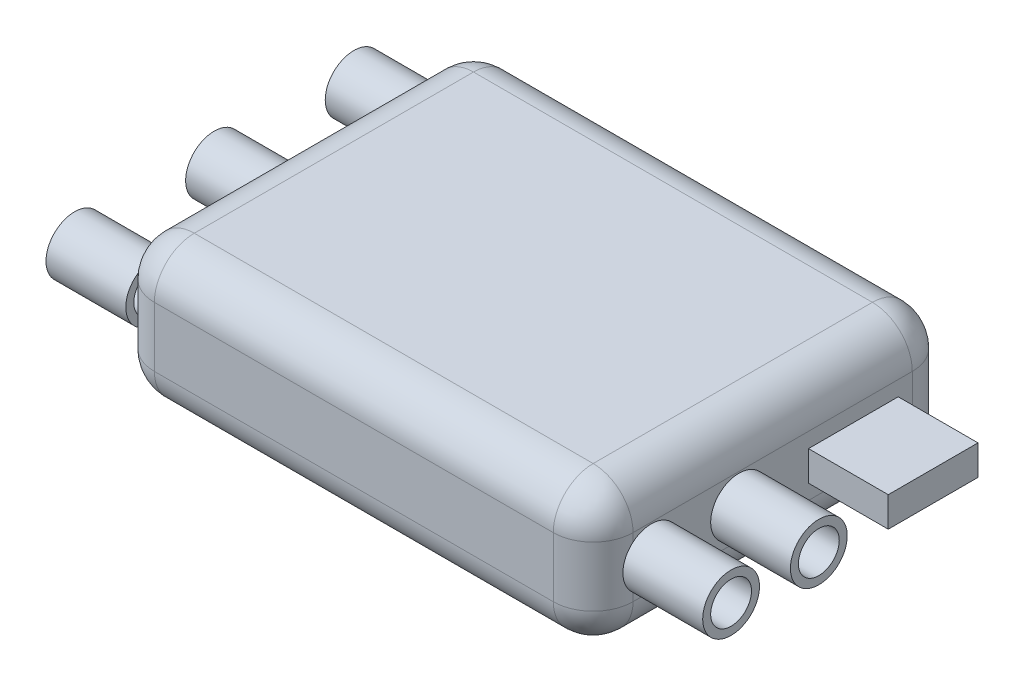
SolidWorks part; units mm, degrees
ref_plane "Front Plane" through (0, 0, 0) normal (0, 0, 1) x (1, 0, 0)
ref_plane "Top Plane" through (0, 0, 0) normal (0, 1, 0) x (1, 0, 0)
ref_plane "Right Plane" through (0, 0, 0) normal (1, 0, 0) x (0, 0, -1)
sketch "Sketch1" plane through (0, 0, 0) normal (0, 1, 0) x (1, 0, 0)
  line L1 (-10, 9) -> (10, 9)
  line L2 (-12, 7) -> (-12, -7)
  line L3 (-10, -9) -> (10, -9)
  line L4 (12, 7) -> (12, -7)
  line L5 (-12, 9) -> (12, -9) construction
  line L6 (-12, -9) -> (12, 9) construction
  arc A0 (10, -9) -> (12, -7) centre (10, -7) ccw
  arc A1 (-12, -7) -> (-10, -9) centre (-10, -7) ccw
  arc A2 (10, 9) -> (12, 7) centre (10, 7) cw
  arc A3 (-10, 9) -> (-12, 7) centre (-10, 7) ccw
  point P0 (0, 0)
  dimension "D3" = 2
  dimension "D1" = 24
  dimension "D2" = 18
extrude "Boss-Extrude1" add sketch "Sketch1" along normal blind 7
fillet "Fillet1" radius 2 16 edges at (12, 0, 0) (11.4142, 0, -8.4142) (0, 0, -9) (-11.4142, 0, -8.4142) (-12, 0, 0) (-11.4142, 0, 8.4142) (0, 0, 9) (11.4142, 0, 8.4142) (0, 7, 9) (-11.4142, 7, 8.4142) (-12, 7, 0) (-11.4142, 7, -8.4142) (0, 7, -9) (11.4142, 7, -8.4142) (12, 7, 0) (11.4142, 7, 8.4142)
sketch "Sketch2" plane through (-12, 0, 0) normal (-1, 0, 0) x (0, 0, 1)
  line L0 (-7, 3.5) -> (7, 3.5) construction
  line L1 (-7, 5) -> (-7, 2) construction
  line L2 (7, 5) -> (7, 2) construction
  circle A0 centre (-7, 3.5) radius 1.0342
  circle A1 centre (-7, 3.5) radius 1.4342
  circle A2 centre (0, 3.5) radius 1.0342
  circle A3 centre (0, 3.5) radius 1.4342
  circle A4 centre (7, 3.5) radius 1.0342
  circle A5 centre (7, 3.5) radius 1.4342
  dimension "D1" = 0.4
extrude "Boss-Extrude2" add sketch "Sketch2" along normal blind 4
sketch "Sketch3" plane through (12, 0, 0) normal (1, 0, 0) x (0, 0, -1)
  line L0 (-7, 3.5) -> (7, 3.5) construction
  line L1 (-7, 5) -> (-7, 2) construction
  line L2 (7, 5) -> (7, 2) construction
  line L4 (1.795, 4.25) -> (6.295, 4.25)
  line L5 (1.795, 4.25) -> (1.795, 2.75)
  line L6 (1.795, 2.75) -> (6.295, 2.75)
  line L7 (6.295, 4.25) -> (6.295, 2.75)
  line L8 (1.795, 4.25) -> (6.295, 2.75) construction
  line L9 (1.795, 2.75) -> (6.295, 4.25) construction
  circle A0 centre (-6.0852, 3.5) radius 1.0236
  circle A1 centre (-6.0852, 3.5) radius 1.4236
  circle A2 centre (-1.6852, 3.5) radius 1.0236
  circle A3 centre (-1.6852, 3.5) radius 1.4236
  point P6 (4.045, 3.5)
  dimension "D3" = 2.8472
  dimension "D4" = 0.4
  dimension "D1" = 4.5
  dimension "D2" = 1.5
  dimension "D5" = 4.4
extrude "Boss-Extrude3" add sketch "Sketch3" along normal blind 4
